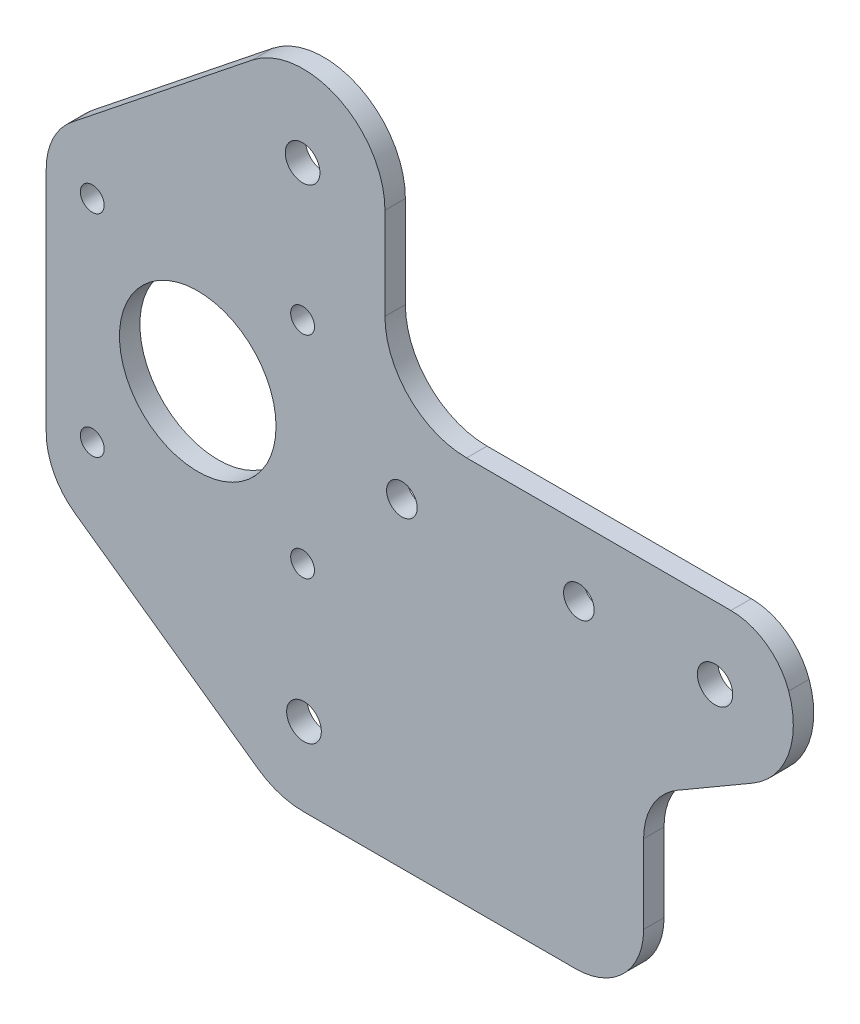
SolidWorks part; units mm, degrees
ref_plane "Front Plane" through (0, 0, 0) normal (0, 0, 1) x (1, 0, 0)
ref_plane "Top Plane" through (0, 0, 0) normal (0, 1, 0) x (1, 0, 0)
ref_plane "Right Plane" through (0, 0, 0) normal (1, 0, 0) x (0, 0, -1)
sketch "Sketch1" plane through (0, 0, 0) normal (0, 0, 1) x (1, 0, 0)
  line L0 (-17.6679, 51.2606) -> (-17.6679, 17.6906)
  line L1 (-13.9043, 59.0777) -> (12.6113, 80.2316)
  line L2 (32.095, 70.8511) -> (32.095, 57.3511)
  line L3 (44.095, 45.3511) -> (82.925, 45.3511)
  line L4 (86.1318, 24.9825) -> (75.0691, 18.5438)
  line L5 (70.0993, 9.9011) -> (70.0993, -1.6489)
  line L6 (60.0993, -11.6489) -> (20.0993, -11.6489)
  line L7 (13.45, -9.5317) -> (-13.45, 9.5317)
  arc A0 (12.6113, 80.2316) -> (32.095, 70.8511) centre (20.095, 70.8511) cw
  arc A3 (-17.6679, 51.2606) -> (-13.9043, 59.0777) centre (-7.6679, 51.2606) cw
  arc A4 (44.095, 45.3511) -> (32.095, 57.3511) centre (44.095, 57.3511) cw
  arc A5 (70.0993, 9.9011) -> (75.0691, 18.5438) centre (80.0993, 9.9011) cw
  arc A6 (20.0993, -11.6489) -> (13.45, -9.5317) centre (20.0993, -0.1489) cw
  arc A7 (-13.45, 9.5317) -> (-17.6679, 17.6906) centre (-7.6679, 17.6906) cw
  arc A8 (70.0993, -1.6489) -> (60.0993, -11.6489) centre (60.0993, -1.6489) cw
  arc A9 (82.925, 45.3511) -> (91.4131, 39.343) centre (82.925, 36.3511) cw
  arc A10 (91.4131, 39.343) -> (86.1318, 24.9825) centre (80.0956, 35.3538) cw
  circle A11 centre (80.5948, 34.7807) radius 2.6
  circle A12 centre (60.5848, 35.3511) radius 2.25
  circle A13 centre (4.5921, 35.3483) radius 11.5
  circle A14 centre (19.995, 70.851) radius 2.55
  circle A15 centre (34.5848, 35.3414) radius 2.2509
  circle A16 centre (20.1993, -0.149) radius 2.55
  circle A17 centre (19.9921, 19.8511) radius 1.75
  circle A18 centre (-10.9079, 19.8511) radius 1.75
  circle A19 centre (-10.9079, 50.8511) radius 1.75
  circle A20 centre (19.9921, 50.8511) radius 1.75
  point P14 (-17.6679, 56.0752)
  point P25 (-17.6679, 12.5209)
  dimension "D3" = 10
  dimension "D4" = 12
  dimension "D5" = 12
  dimension "D6" = 10
  dimension "D7" = 11.5
  dimension "D8" = 10
  dimension "D9" = 10
  dimension "D13" = 5.2
  dimension "D14" = 9
  dimension "D16" = 13.5
  dimension "D12" = 12.8
  dimension "D21" = 12
  dimension "D25" = 4.5
  dimension "D28" = 23
  dimension "D31" = 5.1
  dimension "D34" = 4.5018
  dimension "D37" = 5.1
  dimension "D40" = 3.5
  dimension "D43" = 3.5
  dimension "D46" = 3.5
  dimension "D48" = 3.5
  dimension "D10" = 40
  dimension "D11" = 11.55
  dimension "D15" = 38.83
  dimension "D17" = 57
  dimension "D18" = 32.97
  dimension "D19" = 33.92
  dimension "D20" = 120.2
  dimension "D22" = 33.57
  dimension "D23" = 2.81
  dimension "D24" = 0.76
  dimension "D26" = 20.01
  dimension "D27" = 10
  dimension "D29" = 22.26
  dimension "D30" = 38.74
  dimension "D32" = 38.7
  dimension "D33" = 0.1
  dimension "D35" = 26
  dimension "D36" = 38.39
  dimension "D38" = 0.1
  dimension "D39" = 71
  dimension "D41" = 31.5
  dimension "D42" = 37.66
  dimension "D44" = 31.5
  dimension "D45" = 6.76
  dimension "D47" = 62.5
extrude "Boss-Extrude1" add sketch "Sketch1" along normal blind 3
